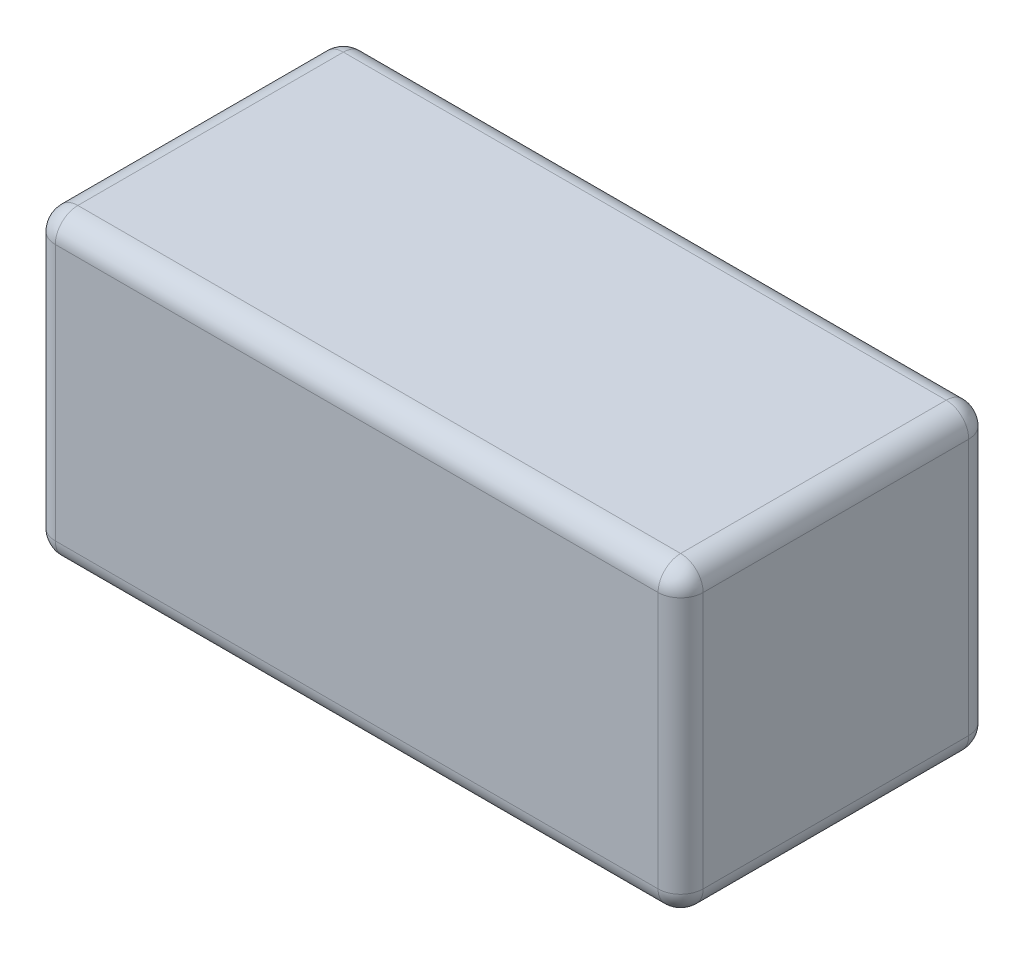
SolidWorks part; units mm, degrees
ref_plane "Front Plane" through (0, 0, 0) normal (0, 0, 1) x (1, 0, 0)
ref_plane "Top Plane" through (0, 0, 0) normal (0, 1, 0) x (1, 0, 0)
ref_plane "Right Plane" through (0, 0, 0) normal (1, 0, 0) x (0, 0, -1)
sketch "Sketch1" plane through (0, 0, 0) normal (0, 0, 1) x (1, 0, 0)
  line L1 (36.5, -17) -> (-36.5, -17)
  line L2 (36.5, -17) -> (36.5, 17)
  line L3 (36.5, 17) -> (-36.5, 17)
  line L4 (-36.5, -17) -> (-36.5, 17)
  line L5 (36.5, -17) -> (-36.5, 17) construction
  line L6 (36.5, 17) -> (-36.5, -17) construction
  point P0 (0, 0)
  dimension "D1" = 34
  dimension "D2" = 73
extrude "Boss-Extrude1" add sketch "Sketch1" along normal blind 35
fillet "Fillet1" radius 2.54 12 edges at (-36.5, 0, 0) (-36.5, -17, 17.5) (0, -17, 0) (36.5, -17, 17.5) (36.5, 0, 0) (36.5, 0, 35) (0, -17, 35) (-36.5, 0, 35) (36.5, 17, 17.5) (0, 17, 35) (-36.5, 17, 17.5) (0, 17, 0)
